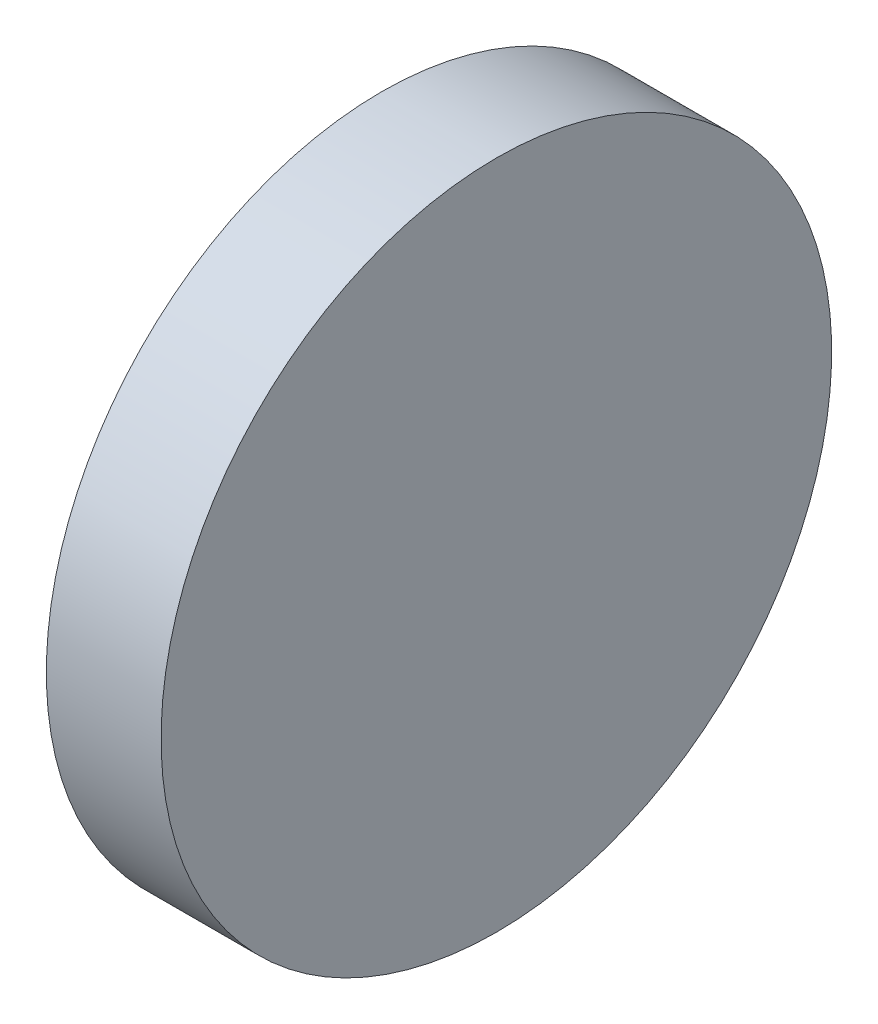
SolidWorks part; units mm, degrees
material "BUTYL"
ref_plane "Front Plane" through (0, 0, 0) normal (0, 0, 1) x (1, 0, 0)
ref_plane "Top Plane" through (0, 0, 0) normal (0, 1, 0) x (1, 0, 0)
ref_plane "Right Plane" through (0, 0, 0) normal (1, 0, 0) x (0, 0, -1)
sketch "Sketch1" plane through (-412.1166, 0, 0) normal (1, 0, 0) x (0, 0, -1)
  circle A0 centre (-214.6592, 41.8496) radius 66.3424 construction
  circle A1 centre (-214.6592, 41.8496) radius 66.3424
  circle A2 centre (-214.6592, 41.8496) radius 74.2235
extrude "Boss-Extrude1" add sketch "Sketch1" against normal up to surface (25.4 mm away) contours A1 | A2 A1
ref_point "Point1"
